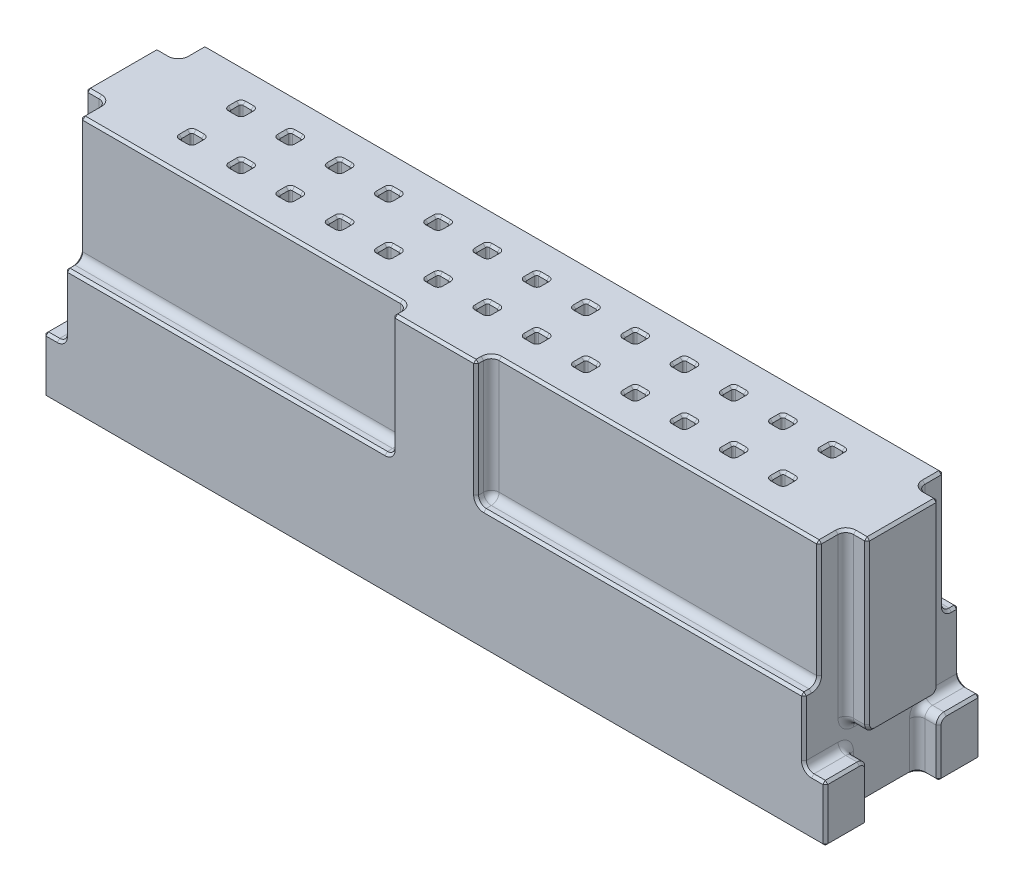
SolidWorks part; units mm, degrees
ref_plane "Front Plane" through (0, 0, 0) normal (0, 0, 1) x (1, 0, 0)
ref_plane "Top Plane" through (0, 0, 0) normal (0, 1, 0) x (1, 0, 0)
ref_plane "Right Plane" through (0, 0, 0) normal (1, 0, 0) x (0, 0, -1)
sketch "Sketch1" plane through (0, 0, 0) normal (0, 1, 0) x (1, 0, 0)
  line L1 (-20.1549, -4.0005) -> (20.1549, -4.0005)
  line L2 (-20.1549, -4.0005) -> (-20.1549, 4.0005)
  line L3 (-20.1549, 4.0005) -> (20.1549, 4.0005)
  line L4 (20.1549, -4.0005) -> (20.1549, 4.0005)
  line L5 (-20.1549, -4.0005) -> (20.1549, 4.0005) construction
  line L6 (-20.1549, 4.0005) -> (20.1549, -4.0005) construction
  point P0 (0, 0)
  dimension "D1" = 40.3098
  dimension "D2" = 8.001
extrude "Boss-Extrude1" add sketch "Sketch1" along normal blind 12.7 contours L3 L4 L1 L2
sketch "Sketch2" plane through (0, 12.7, 0) normal (0, 1, 0) x (1, 0, 0)
  line L1 (-20.1549, 4.0005) -> (-19.05, 4.0005)
  line L2 (-20.1549, 4.0005) -> (-20.1549, 1.8415)
  line L3 (-20.1549, 1.8415) -> (-19.05, 1.8415)
  line L4 (-19.05, 4.0005) -> (-19.05, 1.8415)
  line L5 (-20.1549, -4.0005) -> (-19.05, -4.0005)
  line L6 (-20.1549, -4.0005) -> (-20.1549, -1.8415)
  line L7 (-20.1549, -1.8415) -> (-19.05, -1.8415)
  line L8 (-19.05, -4.0005) -> (-19.05, -1.8415)
  line L9 (20.1549, 4.0005) -> (19.05, 4.0005)
  line L10 (20.1549, 4.0005) -> (20.1549, 1.8415)
  line L11 (20.1549, 1.8415) -> (19.05, 1.8415)
  line L12 (19.05, 4.0005) -> (19.05, 1.8415)
  line L13 (20.1549, -4.0005) -> (19.05, -4.0005)
  line L14 (20.1549, -4.0005) -> (20.1549, -1.8415)
  line L15 (20.1549, -1.8415) -> (19.05, -1.8415)
  line L16 (19.05, -4.0005) -> (19.05, -1.8415)
  dimension "D1" = 1.1049
  dimension "D2" = 2.159
extrude "Cut-Extrude1" cut sketch "Sketch2" against normal blind 9.7993
sketch "Sketch4" plane through (0, 12.7, 0) normal (0, 1, 0) x (1, 0, 0)
  line L1 (-20.1549, -1.8415) -> (-19.05, -1.8415)
  line L2 (-20.1549, -1.8415) -> (-20.1549, 1.8415)
  line L3 (-20.1549, 1.8415) -> (-19.05, 1.8415)
  line L4 (-19.05, -1.8415) -> (-19.05, 1.8415)
  line L5 (20.1549, -1.8415) -> (19.05, -1.8415)
  line L6 (20.1549, -1.8415) -> (20.1549, 1.8415)
  line L7 (20.1549, 1.8415) -> (19.05, 1.8415)
  line L8 (19.05, -1.8415) -> (19.05, 1.8415)
extrude "Cut-Extrude2" cut sketch "Sketch4" against normal up to next from offset 8.7312 offset against normal yes
sketch "Sketch5" plane through (0, 12.7, 0) normal (0, 1, 0) x (1, 0, 0)
  line L0 (19.05, -1.8415) -> (19.05, -4.0005) construction
  line L1 (-19.05, -4.0005) -> (-2.1501, -4.0005)
  line L2 (-19.05, -4.0005) -> (-19.05, -3.2144)
  line L3 (-19.05, -3.2144) -> (-2.1501, -3.2144)
  line L4 (19.05, -4.0005) -> (19.05, -3.2144)
  line L5 (19.05, 4.0005) -> (19.05, 1.8415) construction
  line L6 (-19.05, 4.0005) -> (19.05, 4.0005)
  line L7 (-19.05, 4.0005) -> (-19.05, 3.2144)
  line L8 (-19.05, 3.2144) -> (19.05, 3.2144)
  line L9 (19.05, 4.0005) -> (19.05, 3.2144)
  line L10 (0, -3.2144) -> (0, 3.2144) construction
  line L11 (-2.1501, -3.2144) -> (-2.1501, -4.0005)
  line L12 (2.1501, -3.2144) -> (2.1501, -4.0005)
  line L13 (2.1501, -3.6074) -> (-2.1501, -3.6074) construction
  line L14 (0, -3.6074) -> (0, -3.2144) construction
  line L15 (2.1501, -3.2144) -> (19.05, -3.2144)
  line L16 (2.1501, -4.0005) -> (19.05, -4.0005)
  dimension "D1" = 6.4287
  dimension "D2" = 4.3002
extrude "Cut-Extrude3" cut sketch "Sketch5" against normal blind 6.4008 contours L8 L9 L6 L7
sketch "Sketch6" plane through (0, 12.7, 0) normal (0, 1, 0) x (1, 0, 0)
  line L0 (-20.1549, -1.8415) -> (-20.1549, 1.8415) construction
  line L1 (-15.5499, 0.9601) -> (-14.9301, 0.9601)
  line L2 (-15.5499, 0.9601) -> (-15.5499, 1.5799)
  line L3 (-15.5499, 1.5799) -> (-14.9301, 1.5799)
  line L4 (-14.9301, 0.9601) -> (-14.9301, 1.5799)
  line L5 (-15.5499, 0.9601) -> (-14.9301, 1.5799) construction
  line L6 (-15.5499, 1.5799) -> (-14.9301, 0.9601) construction
  line L7 (19.05, 4.0005) -> (-19.05, 4.0005) construction
  point P0 (-15.24, 1.27)
  dimension "D1" = 0.6198
  dimension "D2" = 4.605
  dimension "D3" = 2.4206
extrude "Cut-Extrude4" cut sketch "Sketch6" against normal blind 6.1011 contours L1 L4 L3 L2
pattern_linear "LPattern1" count 13 spacing 2.54 along (1, 0, 0) count 2 spacing 2.54 along (0, 0, 1) of "Cut-Extrude4"
fillet "Fillet1" radius 0.3969 29 edges at (19.05, 8.3344, -1.8415) (19.05, 8.3344, 1.8415) (-19.05, 8.3344, 1.8415) (-19.05, 8.3344, -1.8415) (0, 6.2992, -3.2144) (-10.6001, 6.2992, 3.2144) (-2.1501, 6.2992, 3.6074) (-2.1501, 9.4996, 3.2144) (2.1501, 6.2992, 3.6074) (10.6001, 6.2992, 3.2144) (2.1501, 9.4996, 3.2144) (-19.05, 3.9688, 0) (19.05, 3.9688, 0) (-19.6025, 3.9688, 1.8415) (-19.6025, 3.9688, -1.8415) (-19.6025, 2.9007, -1.8415) (-19.6025, 2.9007, 1.8415) (19.6024, 3.9688, 1.8415) (19.6024, 3.9688, -1.8415) (19.6024, 2.9007, 1.8415) (19.6024, 2.9007, -1.8415) (19.05, 1.4503, -1.8415) (19.05, 2.9007, -2.921) (19.05, 1.4503, 1.8415) (19.05, 2.9007, 2.921) (-19.05, 2.9007, 2.921) (-19.05, 1.4503, 1.8415) (-19.05, 1.4503, -1.8415) (-19.05, 2.9007, -2.921)
fillet "Fillet3" radius 0.0992 44 edges at (13.0099, 9.6495, 1.5799) (9.8501, 9.6495, 0.9601) (7.3101, 9.6495, 0.9601) (5.3899, 9.6495, 0.9601) (2.8499, 9.6495, 1.5799) (-0.3099, 9.6495, 1.5799) (-0.3099, 9.6495, 0.9601) (-2.2301, 9.6495, 1.5799) (-2.8499, 9.6495, 0.9601) (-5.3899, 9.6495, 0.9601) (-7.3101, 9.6495, 1.5799) (-7.3101, 9.6495, 0.9601) (-7.9299, 9.6495, 0.9601) (-10.4699, 9.6495, 1.5799) (-12.3901, 9.6495, 0.9601) (14.9301, 9.6495, -1.5799) (4.7701, 9.6495, -1.5799) (2.2301, 9.6495, -0.9601) (2.2301, 9.6495, -1.5799) (-2.8499, 9.6495, -0.9601) (-4.7701, 9.6495, -1.5799) (-7.3101, 9.6495, -1.5799) (-14.9301, 9.6495, -1.5799) (15.5499, 9.6495, 1.5799) (5.08, 6.5989, -1.5799) (7.62, 6.5989, -1.5799) (10.4699, 6.5989, -1.27) (10.16, 6.5989, -0.9601) (13.0099, 6.5989, -1.27) (-14.9301, 6.5989, 1.27) (-10.16, 6.5989, 0.9601) (-9.8501, 6.5989, 1.27) (-7.9299, 6.5989, 1.27) (-7.3101, 6.5989, 1.27) (-7.62, 6.5989, 1.5799) (-5.3899, 6.5989, 1.27) (-4.7701, 6.5989, 1.27) (-5.08, 6.5989, 1.5799) (7.62, 6.5989, 0.9601) (7.9299, 6.5989, 1.27) (-10.16, 6.5989, -0.9601) (-9.8501, 6.5989, -1.27) (-12.3901, 6.5989, -1.27) (-15.24, 6.5989, -1.5799)
chamfer "Chamfer1" distance 0.127 angle 45 303 edges at (15.5208, 12.7, 1.5508) (15.5499, 12.7, 1.27) (15.5208, 12.7, 0.9892) (15.24, 12.7, 0.9601) (14.9592, 12.7, 0.9892) (14.9301, 12.7, 1.27) (14.9592, 12.7, 1.5508) (15.24, 12.7, 1.5799) (12.9808, 12.7, 1.5508) (13.0099, 12.7, 1.27) (12.9808, 12.7, 0.9892) (12.7, 12.7, 0.9601) (12.4192, 12.7, 0.9892) (12.3901, 12.7, 1.27) (12.4192, 12.7, 1.5508) (12.7, 12.7, 1.5799) (10.4408, 12.7, 1.5508) (10.4699, 12.7, 1.27) (10.4408, 12.7, 0.9892) (10.16, 12.7, 0.9601) (9.8792, 12.7, 0.9892) (9.8501, 12.7, 1.27) (9.8792, 12.7, 1.5508) (10.16, 12.7, 1.5799) (7.9008, 12.7, 1.5508) (7.9299, 12.7, 1.27) (7.9008, 12.7, 0.9892) (7.62, 12.7, 0.9601) (7.3392, 12.7, 0.9892) (7.3101, 12.7, 1.27) (7.3392, 12.7, 1.5508) (7.62, 12.7, 1.5799) (5.3608, 12.7, 1.5508) (5.3899, 12.7, 1.27) (5.3608, 12.7, 0.9892) (5.08, 12.7, 0.9601) (4.7992, 12.7, 0.9892) (4.7701, 12.7, 1.27) (4.7992, 12.7, 1.5508) (5.08, 12.7, 1.5799) (2.8208, 12.7, 1.5508) (2.8499, 12.7, 1.27) (2.8208, 12.7, 0.9892) (2.54, 12.7, 0.9601) (2.2592, 12.7, 0.9892) (2.2301, 12.7, 1.27) (2.2592, 12.7, 1.5508) (2.54, 12.7, 1.5799) (0.2808, 12.7, 1.5508) (0.3099, 12.7, 1.27) (0.2808, 12.7, 0.9892) (0, 12.7, 0.9601) (-0.2808, 12.7, 0.9892) (-0.3099, 12.7, 1.27) (-0.2808, 12.7, 1.5508) (0, 12.7, 1.5799) (-2.2592, 12.7, 1.5508) (-2.2301, 12.7, 1.27) (-2.2592, 12.7, 0.9892) (-2.54, 12.7, 0.9601) (-2.8208, 12.7, 0.9892) (-2.8499, 12.7, 1.27) (-2.8208, 12.7, 1.5508) (-2.54, 12.7, 1.5799) (-4.7992, 12.7, 1.5508) (-4.7701, 12.7, 1.27) (-4.7992, 12.7, 0.9892) (-5.08, 12.7, 0.9601) (-5.3608, 12.7, 0.9892) (-5.3899, 12.7, 1.27) (-5.3608, 12.7, 1.5508) (-5.08, 12.7, 1.5799) (-7.3392, 12.7, 1.5508) (-7.3101, 12.7, 1.27) (-7.3392, 12.7, 0.9892) (-7.62, 12.7, 0.9601) (-7.9008, 12.7, 0.9892) (-7.9299, 12.7, 1.27) (-7.9008, 12.7, 1.5508) (-7.62, 12.7, 1.5799) (-9.8792, 12.7, 1.5508) (-9.8501, 12.7, 1.27) (-9.8792, 12.7, 0.9892) (-10.16, 12.7, 0.9601) (-10.4408, 12.7, 0.9892) (-10.4699, 12.7, 1.27) (-10.4408, 12.7, 1.5508) (-10.16, 12.7, 1.5799) (-12.4192, 12.7, 1.5508) (-12.3901, 12.7, 1.27) (-12.4192, 12.7, 0.9892) (-12.7, 12.7, 0.9601) (-12.9808, 12.7, 0.9892) (-13.0099, 12.7, 1.27) (-12.9808, 12.7, 1.5508) (-12.7, 12.7, 1.5799) (-14.9592, 12.7, 1.5508) (-14.9301, 12.7, 1.27) (-14.9592, 12.7, 0.9892) (-15.24, 12.7, 0.9601) (-15.5208, 12.7, 0.9892) (-15.5499, 12.7, 1.27) (-15.5208, 12.7, 1.5508) (-15.24, 12.7, 1.5799) (15.5208, 12.7, -0.9892) (15.5499, 12.7, -1.27) (15.5208, 12.7, -1.5508) (15.24, 12.7, -1.5799) (14.9592, 12.7, -1.5508) (14.9301, 12.7, -1.27) (14.9592, 12.7, -0.9892) (15.24, 12.7, -0.9601) (12.9808, 12.7, -0.9892) (13.0099, 12.7, -1.27) (12.9808, 12.7, -1.5508) (12.7, 12.7, -1.5799) (12.4192, 12.7, -1.5508) (12.3901, 12.7, -1.27) (12.4192, 12.7, -0.9892) (12.7, 12.7, -0.9601) (10.4408, 12.7, -0.9892) (10.4699, 12.7, -1.27) (10.4408, 12.7, -1.5508) (10.16, 12.7, -1.5799) (9.8792, 12.7, -1.5508) (9.8501, 12.7, -1.27) (9.8792, 12.7, -0.9892) (10.16, 12.7, -0.9601) (7.9008, 12.7, -0.9892) (7.9299, 12.7, -1.27) (7.9008, 12.7, -1.5508) (7.62, 12.7, -1.5799) (7.3392, 12.7, -1.5508) (7.3101, 12.7, -1.27) (7.3392, 12.7, -0.9892) (7.62, 12.7, -0.9601) (5.3608, 12.7, -0.9892) (5.3899, 12.7, -1.27) (5.3608, 12.7, -1.5508) (5.08, 12.7, -1.5799) (4.7992, 12.7, -1.5508) (4.7701, 12.7, -1.27) (4.7992, 12.7, -0.9892) (5.08, 12.7, -0.9601) (2.8208, 12.7, -0.9892) (2.8499, 12.7, -1.27) (2.8208, 12.7, -1.5508) (2.54, 12.7, -1.5799) (2.2592, 12.7, -1.5508) (2.2301, 12.7, -1.27) (2.2592, 12.7, -0.9892) (2.54, 12.7, -0.9601) (0.2808, 12.7, -0.9892) (0.3099, 12.7, -1.27) (0.2808, 12.7, -1.5508) (0, 12.7, -1.5799) (-0.2808, 12.7, -1.5508) (-0.3099, 12.7, -1.27) (-0.2808, 12.7, -0.9892) (0, 12.7, -0.9601) (-2.2592, 12.7, -0.9892) (-2.2301, 12.7, -1.27) (-2.2592, 12.7, -1.5508) (-2.54, 12.7, -1.5799) (-2.8208, 12.7, -1.5508) (-2.8499, 12.7, -1.27) (-2.8208, 12.7, -0.9892) (-2.54, 12.7, -0.9601) (-4.7992, 12.7, -0.9892) (-4.7701, 12.7, -1.27) (-4.7992, 12.7, -1.5508) (-5.08, 12.7, -1.5799) (-5.3608, 12.7, -1.5508) (-5.3899, 12.7, -1.27) (-5.3608, 12.7, -0.9892) (-5.08, 12.7, -0.9601) (-7.3392, 12.7, -0.9892) (-7.3101, 12.7, -1.27) (-7.3392, 12.7, -1.5508) (-7.62, 12.7, -1.5799) (-7.9008, 12.7, -1.5508) (-7.9299, 12.7, -1.27) (-7.9008, 12.7, -0.9892) (-7.62, 12.7, -0.9601) (-9.8792, 12.7, -0.9892) (-9.8501, 12.7, -1.27) (-9.8792, 12.7, -1.5508) (-10.16, 12.7, -1.5799) (-10.4408, 12.7, -1.5508) (-10.4699, 12.7, -1.27) (-10.4408, 12.7, -0.9892) (-10.16, 12.7, -0.9601) (-12.4192, 12.7, -0.9892) (-12.3901, 12.7, -1.27) (-12.4192, 12.7, -1.5508) (-12.7, 12.7, -1.5799) (-12.9808, 12.7, -1.5508) (-13.0099, 12.7, -1.27) (-12.9808, 12.7, -0.9892) (-12.7, 12.7, -0.9601) (-19.05, 6.2992, -3.8059) (19.05, 6.2992, -3.8059) (-19.05, 6.2992, 3.8059) (19.05, 6.2992, 3.8059) (-19.05, 6.4154, -3.3306) (19.05, 6.4154, -3.3306) (-19.05, 6.4154, 3.3306) (19.05, 6.4154, 3.3306) (-19.1662, 0, 1.7253) (-19.8009, 0, 1.8415) (-19.05, 0, 0) (-19.1662, 0, -1.7253) (-19.8009, 0, -1.8415) (20.1549, 0, -2.921) (-20.1549, 0, -2.921) (-20.1549, 1.2519, -1.8415) (-20.1549, 2.7844, -1.9577) (-20.1549, 2.9007, -3.1194) (-20.1549, 1.4503, -4.0005) (0, 0, -4.0005) (20.1549, 1.4503, -4.0005) (-19.8009, 2.9007, -4.0005) (-19.1662, 3.0169, -4.0005) (-19.05, 4.7984, -4.0005) (0, 6.2992, -4.0005) (19.05, 4.7984, -4.0005) (19.1662, 3.0169, -4.0005) (19.8009, 2.9007, -4.0005) (20.1549, 2.9007, -3.1194) (20.1549, 2.7844, -1.9577) (20.1549, 1.2519, -1.8415) (19.8009, 0, -1.8415) (19.1662, 0, -1.7253) (19.05, 0, 0) (19.1662, 0, 1.7253) (19.8009, 0, 1.8415) (-19.05, 9.698, -3.2144) (19.05, 9.698, -3.2144) (-19.05, 9.698, 3.2144) (20.1549, 0, 2.921) (20.1549, 1.2519, 1.8415) (20.1549, 2.7844, 1.9577) (20.1549, 2.9007, 3.1194) (19.05, 9.698, 3.2144) (-20.1549, 0, 2.921) (-20.1549, 1.2519, 1.8415) (-20.1549, 2.7844, 1.9577) (-20.1549, 2.9007, 3.1194) (20.1549, 8.5328, -1.8415) (20.1549, 4.085, -1.7253) (20.1549, 3.9688, 0) (20.1549, 4.085, 1.7253) (20.1549, 8.5328, 1.8415) (19.05, 4.7984, 4.0005) (19.1662, 3.0169, 4.0005) (19.8009, 2.9007, 4.0005) (20.1549, 1.4503, 4.0005) (0, 0, 4.0005) (-20.1549, 1.4503, 4.0005) (-19.8009, 2.9007, 4.0005) (-19.1662, 3.0169, 4.0005) (-19.05, 4.7984, 4.0005) (-10.7985, 6.2992, 4.0005) (-2.2664, 6.4154, 4.0005) (-2.1501, 9.698, 4.0005) (10.7985, 6.2992, 4.0005) (2.2664, 6.4154, 4.0005) (2.1501, 9.698, 4.0005) (-20.1549, 4.085, -1.7253) (-20.1549, 8.5328, -1.8415) (-20.1549, 3.9688, 0) (-20.1549, 4.085, 1.7253) (-20.1549, 8.5328, 1.8415) (19.1662, 12.7, -1.9577) (19.8009, 12.7, -1.8415) (20.1549, 12.7, 0) (19.8009, 12.7, 1.8415) (19.1662, 12.7, 1.9577) (19.05, 12.7, 2.7264) (10.7985, 12.7, 3.2144) (2.2664, 12.7, 3.3306) (2.1501, 12.7, 3.8059) (0, 12.7, 4.0005) (-2.1501, 12.7, 3.8059) (-2.2664, 12.7, 3.3306) (-10.7985, 12.7, 3.2144) (-19.05, 12.7, 2.7264) (-19.1662, 12.7, 1.9577) (-19.8009, 12.7, 1.8415) (-20.1549, 12.7, 0) (-19.8009, 12.7, -1.8415) (-19.1662, 12.7, -1.9577) (-19.05, 12.7, -2.7264) (0, 12.7, -3.2144) (19.05, 12.7, -2.7264) (-14.9592, 12.7, -0.9892) (-14.9301, 12.7, -1.27) (-14.9592, 12.7, -1.5508) (-15.24, 12.7, -1.5799) (-15.5208, 12.7, -1.5508) (-15.5499, 12.7, -1.27) (-15.5208, 12.7, -0.9892) (-15.24, 12.7, -0.9601)
